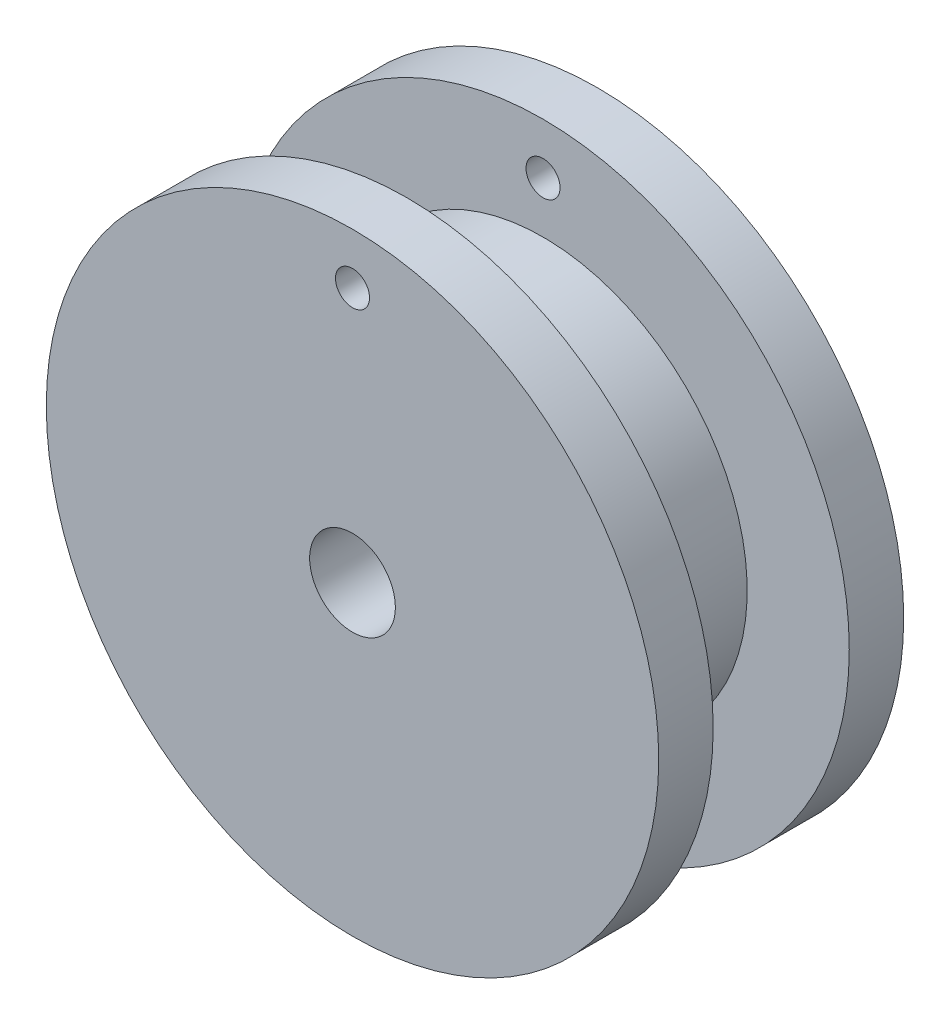
SolidWorks part; units mm, degrees
material "PVC Rigid"
ref_plane "Front Plane" through (0, 0, 0) normal (0, 0, 1) x (1, 0, 0)
ref_plane "Top Plane" through (0, 0, 0) normal (0, 1, 0) x (1, 0, 0)
ref_plane "Right Plane" through (0, 0, 0) normal (1, 0, 0) x (0, 0, -1)
sketch "Sketch1" plane through (0, 0, 0) normal (0, 0, 1) x (1, 0, 0)
  circle A0 centre (0, 0) radius 9.525
  dimension "D1" = 19.05
extrude "Boss-Extrude1" add sketch "Sketch1" along normal blind 6.35
sketch "Sketch2" plane through (0, 0, 6.35) normal (0, 0, 1) x (1, 0, 0)
  circle A0 centre (0, 0) radius 2
  dimension "D1" = 4
extrude "Cut-Extrude1" cut sketch "Sketch2" against normal through all
sketch "Sketch5" plane through (0, 0, 6.35) normal (0, 0, 1) x (1, 0, 0)
  circle A0 centre (0, 0) radius 2 construction
  circle A1 centre (0, 0) radius 2
  circle A2 centre (0, 0) radius 14.2875
  dimension "D1" = 28.575
extrude "Boss-Extrude3" add sketch "Sketch5" along normal blind 2.54
sketch "Sketch6" plane through (0, 0, 0) normal (0, 0, -1) x (-1, 0, 0)
  circle A0 centre (0, 0) radius 2 construction
  circle A1 centre (0, 0) radius 14.2875 construction
  circle A2 centre (0, 0) radius 2
  circle A3 centre (0, 0) radius 14.2875
extrude "Boss-Extrude4" add sketch "Sketch6" along normal blind 2.54
sketch "Sketch7" plane through (0, 0, 8.89) normal (0, 0, 1) x (1, 0, 0)
  line L0 (0, 9.525) -> (0, 11.1125) construction
  line L2 (0, 12.7) -> (0, 14.2875) construction
  circle A0 centre (0, 0) radius 9.525 construction
  circle A1 centre (0, 0) radius 9.525 construction
  circle A2 centre (0, 11.9063) radius 0.7937
  circle A4 centre (0, 0) radius 14.2875 construction
  dimension "D1" = 1.5875
extrude "Cut-Extrude2" cut sketch "Sketch7" against normal through all
